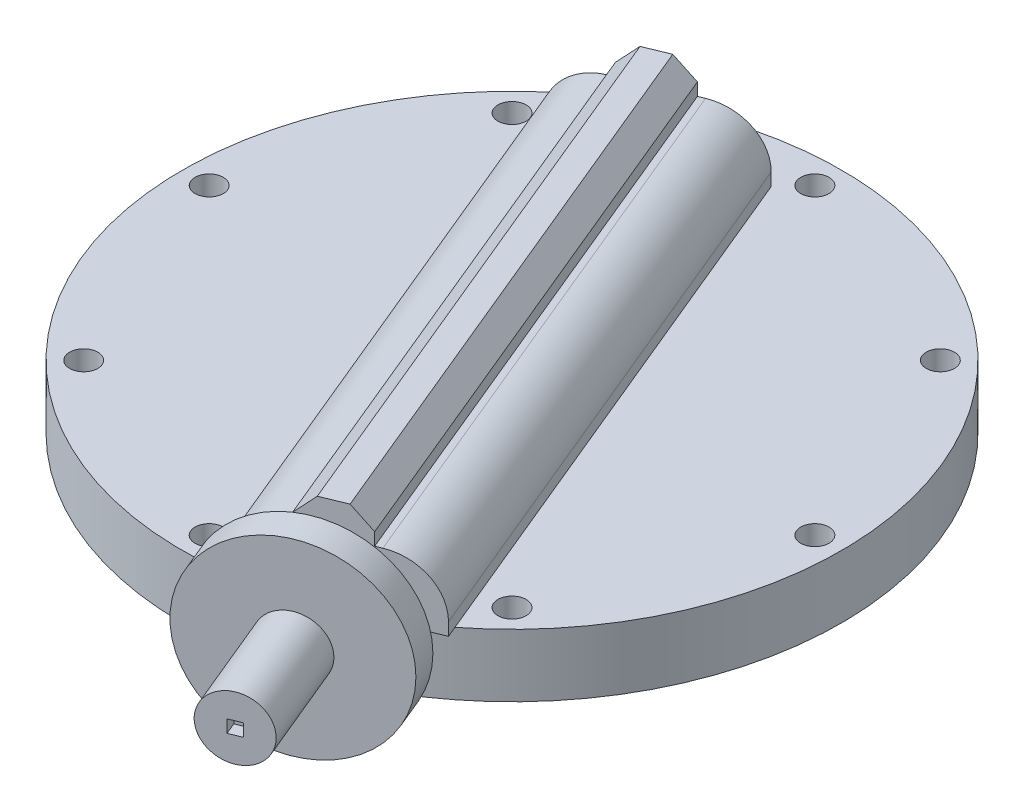
SolidWorks part; units mm, degrees
ref_plane "Front Plane" through (0, 0, 0) normal (0, 0, 1) x (1, 0, 0)
ref_plane "Top Plane" through (0, 0, 0) normal (0, 1, 0) x (1, 0, 0)
ref_plane "Right Plane" through (0, 0, 0) normal (1, 0, 0) x (0, 0, -1)
sketch "Sketch1" plane through (0, 0, 0) normal (0, 1, 0) x (1, 0, 0)
  circle A0 centre (0, 0) radius 66.675
  dimension "D1" = 133.35
extrude "Boss-Extrude1" add sketch "Sketch1" along normal blind 12.7
sketch "Sketch2" plane through (0, 12.7, 0) normal (0, 1, 0) x (1, 0, 0)
  line L0 (0, 0) -> (0, 66.675) construction
  circle A0 centre (0, 0) radius 66.675 construction
  circle A1 centre (0, 61.2775) radius 2.8575
  dimension "D1" = 5.715
  dimension "D2" = 5.3975
extrude "Cut-Extrude1" cut sketch "Sketch2" against normal through all both and the other way through all
pattern_circular "CirPattern1" count 8 over 360 about axis through (0, 0, 0) along (0, 1, 0) of "Cut-Extrude1"
sketch "Sketch4" plane through (0, 12.7, 0) normal (0, 1, 0) x (1, 0, 0)
  line L0 (-66.675, 0) -> (66.675, 0) construction
  line L1 (0, 66.675) -> (0, -66.675) construction
  line L2 (-31.5631, 76.2) -> (31.5631, -76.2) construction
  line L3 (-37.0819, 43.0623) -> (-4.2288, 56.6705)
  line L4 (-37.0819, 43.0623) -> (9.0888, -68.4038)
  line L5 (-4.2288, 56.6705) -> (41.942, -54.7956)
  line L6 (9.0888, -68.4038) -> (41.942, -54.7956)
  circle A0 centre (0, 0) radius 66.675 construction
  point P7 (0, 0)
  point P11 (0, 0)
  point P14 (0, 0)
  point P17 (-20.6553, 49.8664)
  dimension "D4" = 53.975
  dimension "D1" = 67.5
  dimension "D2" = 152.4
  dimension "D3" = 35.56
  dimension "D5" = 120.65
  dimension "D6" = 120.65
extrude "Boss-Extrude2" add sketch "Sketch4" along normal blind 12.7
sketch "Sketch5" plane through (0, 25.4, 0) normal (0, 1, 0) x (1, 0, 0)
  line L0 (-20.6553, 49.8664) -> (25.5154, -61.5997) construction
  line L1 (-4.2288, 56.6705) -> (-37.0819, 43.0623) construction
  line L2 (9.0888, -68.4038) -> (41.942, -54.7956) construction
  line L3 (-26.522, 47.4364) -> (19.6488, -64.0297)
  line L4 (19.6488, -64.0297) -> (31.3821, -59.1696)
  line L5 (31.3821, -59.1696) -> (-14.7887, 52.2964)
  line L6 (-14.7887, 52.2964) -> (-26.522, 47.4364)
  dimension "D1" = 12.7
  dimension "D2" = 6.35
extrude "Boss-Extrude3" add sketch "Sketch5" along normal blind 6.35
chamfer "Chamfer1" distance 3.81 angle 45 2 edges at (8.2967, 31.75, 3.4366) (-3.4366, 31.75, 8.2967)
fillet "Fillet3" radius 10.16 2 edges at (18.8566, 25.4, -0.9375) (-13.9965, 25.4, 12.6707)
ref_plane "Plane1" through (28.9175, 0, 69.813) normal (0.3827, 0, 0.9239) x (0.9239, 0, -0.3827)
sketch "Sketch7" plane through (28.9175, 0, 69.813) normal (0.3827, 0, 0.9239) x (0.9239, 0, -0.3827)
  line L0 (-66.675, 0) -> (66.675, 0) construction
  circle A0 centre (0, 15.875) radius 10.16
  dimension "D1" = 20.32
  dimension "D2" = 15.875
  dimension "D3" = 15.875
extrude "Boss-Extrude4" add sketch "Sketch7" against normal blind 10.16 contours A0
sketch "Sketch8" plane through (28.9175, 0, 69.813) normal (0.3827, 0, 0.9239) x (0.9239, 0, -0.3827)
  line L0 (0, 26.035) -> (0, 15.875) construction
  circle A0 centre (0, 15.875) radius 10.16 construction
  circle A1 centre (0, 15.875) radius 19.05
  dimension "D1" = 38.1
extrude "Boss-Extrude5" add sketch "Sketch8" along normal blind 6.35
sketch "Sketch9" plane through (31.3475, 0, 75.6796) normal (0.3827, 0, 0.9239) x (0.9239, 0, -0.3827)
  circle A0 centre (0, 15.875) radius 6.35
  dimension "D1" = 12.7
extrude "Boss-Extrude6" add sketch "Sketch9" along normal blind 21.59
sketch "Sketch10" plane through (39.6096, 0, 95.6262) normal (0.3827, 0, 0.9239) x (0.9239, 0, -0.3827)
  line L0 (0, 9.525) -> (0, 22.225) construction
  circle A0 centre (0, 15.875) radius 6.35 construction
sketch "Sketch11" plane through (39.6096, 0, 95.6262) normal (0.3827, 0, 0.9239) x (0.9239, 0, -0.3827)
  line L1 (-1.27, 17.145) -> (1.27, 17.145)
  line L2 (-1.27, 17.145) -> (-1.27, 14.605)
  line L3 (-1.27, 14.605) -> (1.27, 14.605)
  line L4 (1.27, 17.145) -> (1.27, 14.605)
  line L5 (-1.27, 17.145) -> (1.27, 14.605) construction
  line L6 (-1.27, 14.605) -> (1.27, 17.145) construction
  point P0 (0, 15.875)
  dimension "D1" = 2.54
  dimension "D2" = 2.54
extrude "Cut-Extrude2" cut sketch "Sketch11" against normal blind 2.54 contours L2 L3 L4 L1
